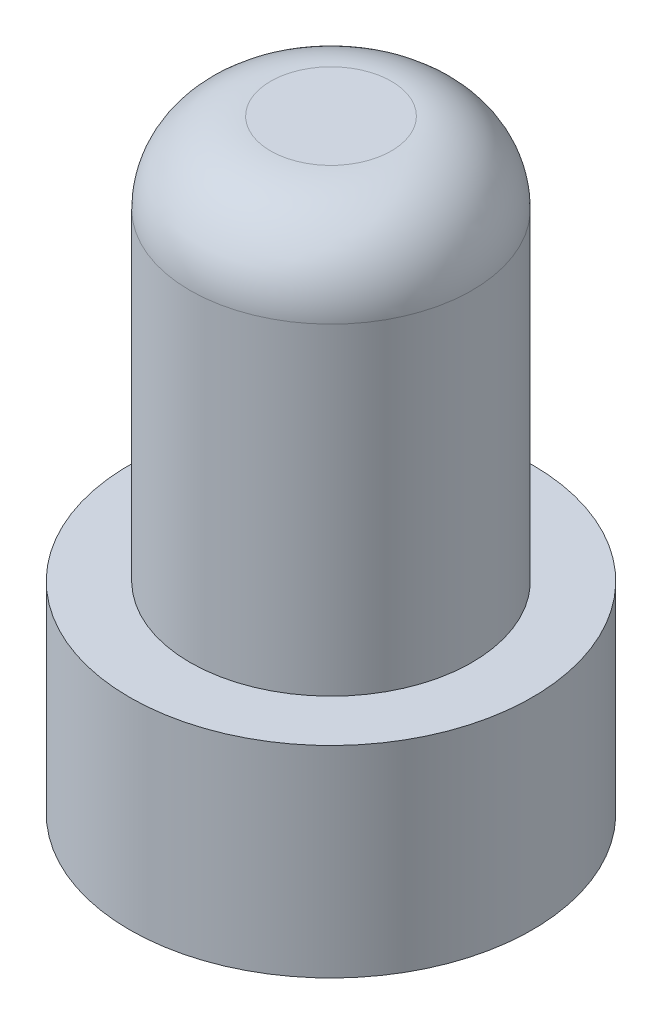
SolidWorks part; units mm, degrees
ref_plane "Front Plane" through (0, 0, 0) normal (0, 0, 1) x (1, 0, 0)
ref_plane "Top Plane" through (0, 0, 0) normal (0, 1, 0) x (1, 0, 0)
ref_plane "Right Plane" through (0, 0, 0) normal (1, 0, 0) x (0, 0, -1)
sketch "Sketch1" plane through (0, 0, 0) normal (0, 1, 0) x (1, 0, 0)
  circle A0 centre (0, 0) radius 2.5
  dimension "D1" = 5
extrude "Boss-Extrude1" add sketch "Sketch1" along normal blind 2.5
sketch "Sketch2" plane through (0, 2.5, 0) normal (0, 1, 0) x (1, 0, 0)
  circle A0 centre (0, 0) radius 1.75
  dimension "D1" = 3.5
extrude "Boss-Extrude2" add sketch "Sketch2" along normal blind 5
fillet "Fillet1" radius 1 1 edges at (0, 7.5, 1.75)
